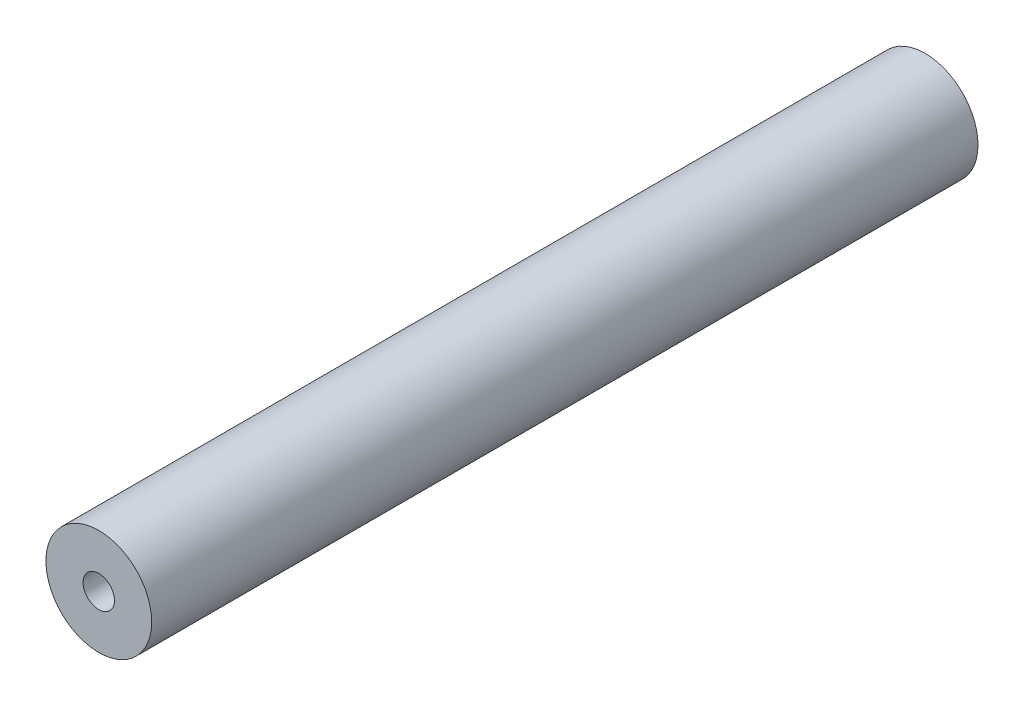
SolidWorks part; units mm, degrees
material "6061-T6 (SS)"
ref_plane "Front Plane" through (0, 0, 0) normal (0, 0, 1) x (1, 0, 0)
ref_plane "Top Plane" through (0, 0, 0) normal (0, 1, 0) x (1, 0, 0)
ref_plane "Right Plane" through (0, 0, 0) normal (1, 0, 0) x (0, 0, -1)
sketch "Sketch1" plane through (0, 0, 0) normal (0, 0, 1) x (1, 0, 0)
  circle A0 centre (0, 0) radius 6.4
  dimension "D1" = 12.8
extrude "Boss-Extrude1" add sketch "Sketch1" along normal blind 100
hole_wizard "#10-24 Tapped Hole1" positions "Sketch2" profile "Sketch3" tap size "#10-24" standard "ANSI Inch"
sketch "Sketch2" plane through (0, 0, 0) normal (0, 0, -1) x (-1, 0, 0)
  point P0 (0, 0)
sketch "Sketch3" plane through (0, 0, 0) normal (1, 0, 0) x (0, 1, 0)
  line L0 (0, 0) -> (0, 13.9708)
  line L1 (0, 13.9708) -> (1.8986, 12.83)
  line L2 (1.8986, 12.83) -> (1.8986, 0)
  line L5 (1.8986, 0) -> (0, 0)
  line L10 (0, 13.9708) -> (-1.8987, 12.83) construction
  line L11 (0, -6.35) -> (0, 107.95) construction
  dimension "Tap Drill Dia." = 3.7973
  dimension "Tap Drill Depth" = 12.83
  dimension "Drill Angle" = 118
hole_wizard "#10-24 Tapped Hole2" positions "Sketch4" profile "Sketch5" tap size "#10-24" standard "ANSI Inch"
sketch "Sketch4" plane through (0, 0, 100) normal (0, 0, 1) x (1, 0, 0)
  point P0 (0, 0)
sketch "Sketch5" plane through (0, 0, 100) normal (1, 0, 0) x (0, -1, 0)
  line L0 (0, 0) -> (0, 13.9708)
  line L1 (0, 13.9708) -> (1.8986, 12.83)
  line L2 (1.8986, 12.83) -> (1.8986, 0)
  line L5 (1.8986, 0) -> (0, 0)
  line L10 (0, 13.9708) -> (-1.8987, 12.83) construction
  line L11 (0, -6.35) -> (0, 107.95) construction
  dimension "Tap Drill Dia." = 3.7973
  dimension "Tap Drill Depth" = 12.83
  dimension "Drill Angle" = 118
